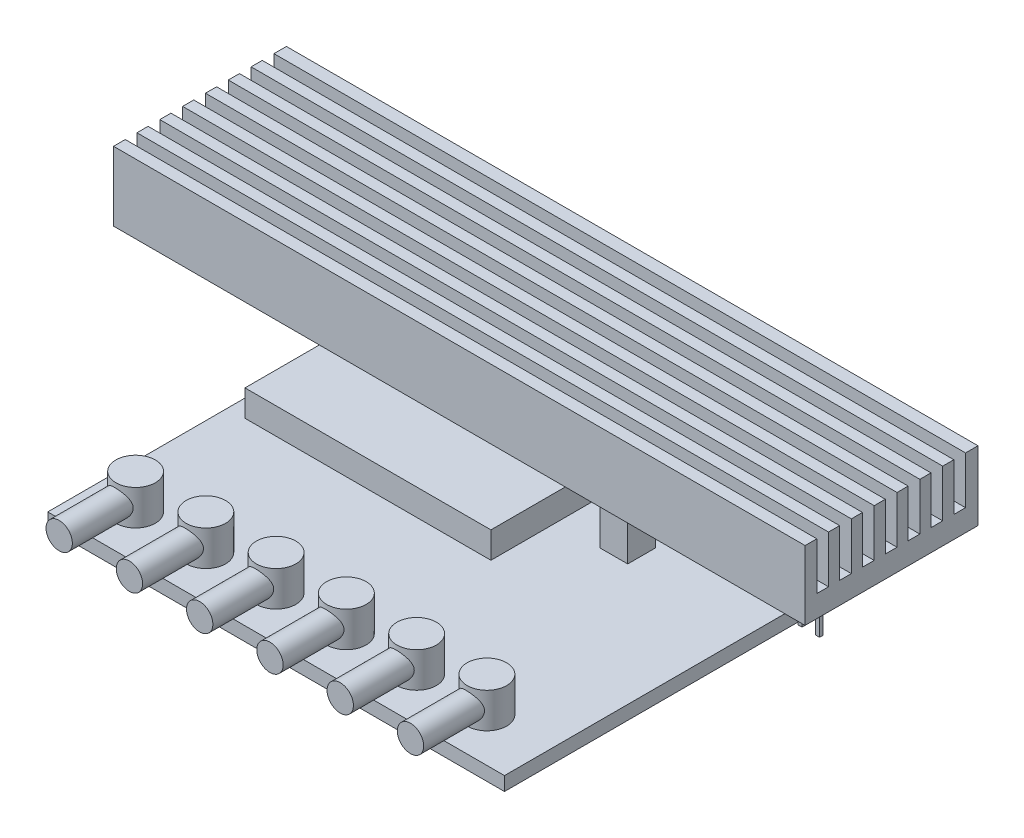
SolidWorks part; units mm, degrees
ref_plane "Front Plane" through (0, 0, 0) normal (0, 0, 1) x (1, 0, 0)
ref_plane "Top Plane" through (0, 0, 0) normal (0, 1, 0) x (1, 0, 0)
ref_plane "Right Plane" through (0, 0, 0) normal (1, 0, 0) x (0, 0, -1)
sketch "Sketch2" plane through (0, 0, 0) normal (0, 0, 1) x (1, 0, 0)
  line L1 (-5, 13.5) -> (5, 13.5)
  line L2 (-5, 13.5) -> (-5, 3.5)
  line L3 (-5, 3.5) -> (5, 3.5)
  line L4 (5, 13.5) -> (5, 3.5)
  dimension "D1" = 5
  dimension "D2" = 10
  dimension "D3" = 10
  dimension "D4" = 3.5
extrude "Boss-Extrude1" add sketch "Sketch2" along normal blind 4.5
sketch "Sketch3" plane through (0, 13.5, 0) normal (0, 1, 0) x (1, 0, 0)
  line L0 (-5.5, 0) -> (5.5, 0) construction
  line L1 (-5, 0) -> (5, 0)
  line L2 (-5, 0) -> (-5, -1.3)
  line L3 (-5, -1.3) -> (5, -1.3)
  line L4 (5, 0) -> (5, -1.3)
  line L5 (5, -4.5) -> (5, 0) construction
  line L7 (-5, -4.5) -> (-5, 0) construction
  dimension "D1" = 1.3
extrude "Boss-Extrude2" add sketch "Sketch3" along normal blind 6.4 separate body
sketch "Sketch4" plane through (0, 3.5, 0) normal (0, -1, 0) x (1, 0, 0)
  line L0 (-5, 4.5) -> (5, 4.5) construction
  line L1 (-0.57, 3) -> (0.57, 3)
  line L2 (-0.57, 3) -> (-0.57, 2.5)
  line L3 (-0.57, 2.5) -> (0.57, 2.5)
  line L4 (0.57, 3) -> (0.57, 2.5)
  point P6 (0, 4.5)
  point P7 (0, 3)
  dimension "D1" = 1.14
  dimension "D2" = 0.5
  dimension "D3" = 2.5
extrude "Boss-Extrude3" add sketch "Sketch4" along normal blind 3.75
sketch "Sketch5" plane through (0, -0.25, 0) normal (0, -1, 0) x (1, 0, 0)
  line L1 (-0.3, 3) -> (0.3, 3)
  line L2 (-0.3, 3) -> (-0.3, 2.5)
  line L3 (-0.3, 2.5) -> (0.3, 2.5)
  line L4 (0.3, 3) -> (0.3, 2.5)
  line L5 (0.57, 3) -> (-0.57, 3) construction
  line L6 (-0.57, 2.5) -> (0.57, 2.5) construction
  point P10 (0, 3)
  point P11 (0, 3)
  dimension "D1" = 0.6
extrude "Boss-Extrude4" add sketch "Sketch5" along normal blind 10 draft 0.03
pattern_linear "LPattern1" count 2 spacing 2.54 along (1, 0, 0) count 2 spacing 2.54 along (-1, 0, 0) of "Boss-Extrude3", "Boss-Extrude4"
pattern_linear "LPattern2" count 4 spacing 15.24 along (1, 0, 0) of bodies 102 105
sketch "Sketch6" plane through (0, 0, 0) normal (0, 1, 0) x (1, 0, 0)
  line L1 (-16.5825, 0) -> (16.5825, 0) construction
  line L2 (-12.7, 12.7) -> (53.34, 12.7)
  line L3 (-12.7, 12.7) -> (-12.7, -53.34)
  line L4 (-12.7, -53.34) -> (53.34, -53.34)
  line L5 (53.34, 12.7) -> (53.34, -53.34)
  line L6 (0, -2.475) -> (0, 2.475) construction
  dimension "D1" = 66.04
  dimension "D2" = 66.04
  dimension "D3" = 12.7
  dimension "D4" = 12.7
extrude "Boss-Extrude5" add sketch "Sketch6" against normal blind 2 separate body
ref_plane "Plane2" through (0, 0, 20.32) normal (0, 0, 1) x (1, 0, 0)
sketch "Sketch7" plane through (0, 0, 0) normal (0, 1, 0) x (1, 0, 0)
  line L0 (53.34, 12.7) -> (-12.7, 12.7) construction
  line L1 (-12.7, 12.7) -> (-12.7, -53.34) construction
  circle A0 centre (-6.35, 6.35) radius 2.8575
  dimension "D1" = 5.715
  dimension "D3" = 6.35
  dimension "D4" = 6.35
extrude "Boss-Extrude6" add sketch "Sketch7" along normal blind 5.08 separate body
ref_plane "Plane1" through (0, 0, -9.2075) normal (0, 0, -1) x (-1, 0, 0)
sketch "Sketch10" plane through (0, 0, -9.2075) normal (0, 0, -1) x (-1, 0, 0)
  line L0 (9.2075, 5.08) -> (3.4925, 5.08) construction
  line L1 (9.2075, 0) -> (9.2075, 5.08) construction
  circle A0 centre (6.4135, 2.4892) radius 1.905
  dimension "D1" = 3.81
  dimension "D3" = 0.889
  dimension "D2" = 2.5908
extrude "Boss-Extrude7" add sketch "Sketch10" along normal blind 8.128 and the other way blind 2.54
mirror "Mirror1" about plane through (0, 0, 20.32) normal (0, 0, 1) of bodies 114
pattern_linear "LPattern3" count 6 spacing 10.16 along (1, 0, 0) of bodies 126 114 120
sketch "Sketch11" plane through (0, 0, 0) normal (0, 1, 0) x (1, 0, 0)
  line L0 (5, -4.5) -> (-5, -4.5) construction
  line L1 (-10.16, -9.58) -> (25.4, -9.58)
  line L2 (-10.16, -9.58) -> (-10.16, -27.36)
  line L3 (-10.16, -27.36) -> (25.4, -27.36)
  line L4 (25.4, -9.58) -> (25.4, -27.36)
  line L5 (-12.7, 12.7) -> (-12.7, -53.34) construction
  dimension "D1" = 17.78
  dimension "D2" = 35.56
  dimension "D3" = 5.08
  dimension "D4" = 2.54
extrude "Boss-Extrude8" add sketch "Sketch11" along normal blind 3.81 separate body
sketch "Sketch12" plane through (0, 0, 0) normal (0, 1, 0) x (1, 0, 0)
  line L0 (25.4, -27.36) -> (25.4, -9.58) construction
  line L1 (31.75, -13.93) -> (35.75, -13.93)
  line L2 (31.75, -13.93) -> (31.75, -17.93)
  line L3 (31.75, -17.93) -> (35.75, -17.93)
  line L4 (35.75, -13.93) -> (35.75, -17.93)
  point P4 (31.75, -15.93)
  point P7 (25.4, -18.47)
  dimension "D1" = 4
  dimension "D2" = 4
  dimension "D3" = 2.54
  dimension "D4" = 6.35
extrude "Boss-Extrude9" add sketch "Sketch12" along normal blind 6.35
sketch "Sketch14" plane through (0, 0, 1.3) normal (0, 0, -1) x (-1, 0, 0)
  line L0 (-50.72, 13.5) -> (-40.72, 13.5) construction
  line L1 (-69.77, 13.5) -> (30.23, 13.5)
  line L2 (-69.77, 13.5) -> (-69.77, 23.5)
  line L3 (-69.77, 23.5) -> (30.23, 23.5)
  line L4 (30.23, 13.5) -> (30.23, 23.5)
  line L5 (-50.72, 19.9) -> (-50.72, 13.5) construction
  dimension "D1" = 100
  dimension "D2" = 10
  dimension "D3" = 0
  dimension "D4" = 19.05
extrude "Boss-Extrude10" add sketch "Sketch14" against normal blind 25 separate body
sketch "Sketch15" plane through (69.77, 0, 0) normal (1, 0, 0) x (0, 0, -1)
  line L0 (-26.3, 23.5) -> (-1.3, 23.5) construction
  line L1 (-24.6067, 23.5) -> (-22.9133, 23.5)
  line L2 (-24.6067, 23.5) -> (-24.6067, 16.642)
  line L3 (-24.6067, 16.642) -> (-22.9133, 16.642)
  line L4 (-22.9133, 23.5) -> (-22.9133, 16.642)
  line L5 (-26.3, 23.5) -> (-26.3, 13.5) construction
  line L6 (-21.3047, 23.5) -> (-21.3047, 16.642)
  line L7 (-21.3047, 23.5) -> (-19.6113, 23.5)
  line L8 (-19.6113, 23.5) -> (-19.6113, 16.642)
  line L9 (-21.3047, 16.642) -> (-19.6113, 16.642)
  line L10 (-18.0027, 23.5) -> (-18.0027, 16.642)
  line L11 (-18.0027, 23.5) -> (-16.3093, 23.5)
  line L12 (-16.3093, 23.5) -> (-16.3093, 16.642)
  line L13 (-18.0027, 16.642) -> (-16.3093, 16.642)
  line L14 (-14.7007, 23.5) -> (-14.7007, 16.642)
  line L15 (-14.7007, 23.5) -> (-13.0073, 23.5)
  line L16 (-13.0073, 23.5) -> (-13.0073, 16.642)
  line L17 (-14.7007, 16.642) -> (-13.0073, 16.642)
  line L18 (-11.3987, 23.5) -> (-11.3987, 16.642)
  line L19 (-11.3987, 23.5) -> (-9.7053, 23.5)
  line L20 (-9.7053, 23.5) -> (-9.7053, 16.642)
  line L21 (-11.3987, 16.642) -> (-9.7053, 16.642)
  line L22 (-8.0967, 23.5) -> (-8.0967, 16.642)
  line L23 (-8.0967, 23.5) -> (-6.4033, 23.5)
  line L24 (-6.4033, 23.5) -> (-6.4033, 16.642)
  line L25 (-8.0967, 16.642) -> (-6.4033, 16.642)
  line L26 (-4.7947, 23.5) -> (-4.7947, 16.642)
  line L27 (-4.7947, 23.5) -> (-3.1013, 23.5)
  line L28 (-3.1013, 23.5) -> (-3.1013, 16.642)
  line L29 (-4.7947, 16.642) -> (-3.1013, 16.642)
  dimension "D1" = 1.6933
  dimension "D2" = 1.6933
  dimension "D3" = 6.858
  dimension "D4" = 7
extrude "Cut-Extrude1" cut sketch "Sketch15" against normal through all
